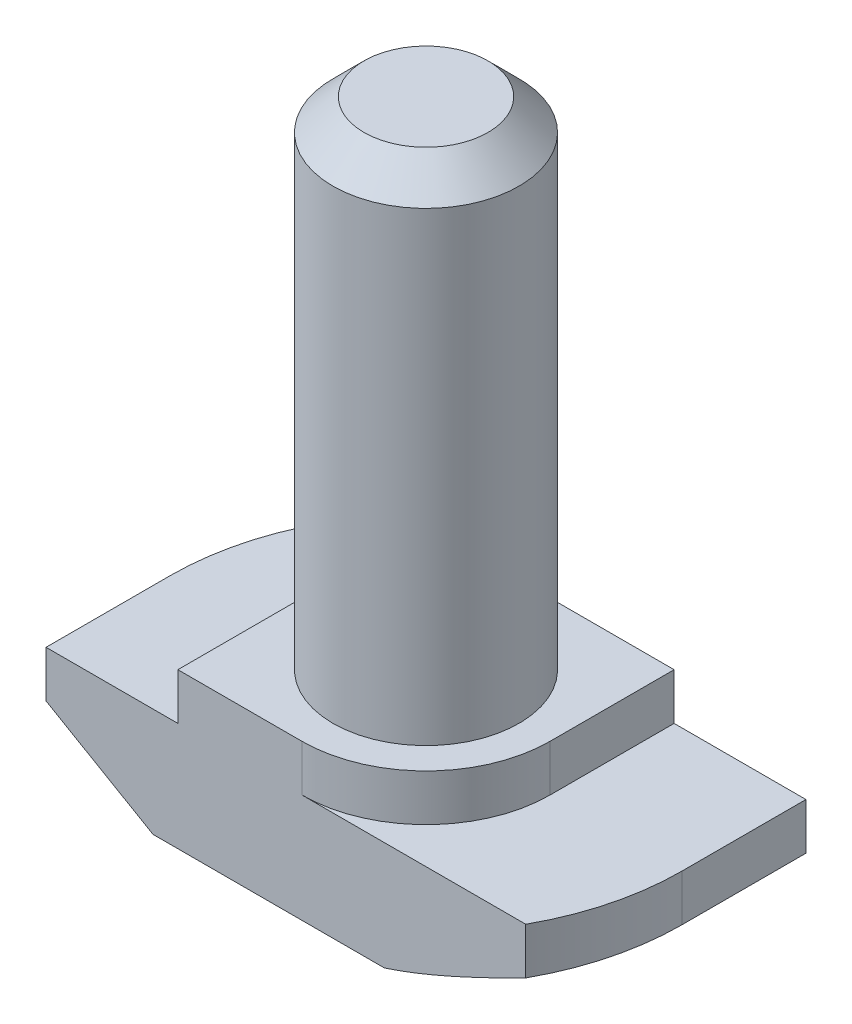
SolidWorks part; units mm, degrees
ref_plane "Спереди" through (0, 0, 0) normal (0, 0, 1) x (1, 0, 0)
ref_plane "Сверху" through (0, 0, 0) normal (0, 1, 0) x (1, 0, 0)
ref_plane "Справа" through (0, 0, 0) normal (1, 0, 0) x (0, 0, -1)
sketch "Эскиз1" plane through (0, 0, 0) normal (0, 0, 1) x (1, 0, 0)
  line L0 (8.25, 0) -> (-8.25, 0)
  line L1 (-8.25, 0) -> (-8.25, 3.5)
  line L2 (-8.25, 3.5) -> (-4, 3.5)
  line L3 (-4, 3.5) -> (-4, 5)
  line L4 (-4, 5) -> (4, 5)
  line L5 (0, 5) -> (0, 0) construction
  line L6 (4, 3.5) -> (4, 5)
  line L7 (8.25, 3.5) -> (4, 3.5)
  line L8 (8.25, 0) -> (8.25, 3.5)
  point P12 (-8.25, 2.6435)
  point P13 (-4, 3.6993)
  dimension "D1" = 8
  dimension "D2" = 16.5
  dimension "D3" = 5
  dimension "D4" = 1.5
extrude "Бобышка-Вытянуть1" add sketch "Эскиз1" along normal mid plane 8
sketch "Эскиз2" plane through (0, 5, 0) normal (0, 1, 0) x (1, 0, 0)
  circle A0 centre (0, 0) radius 3
  dimension "D1" = 6
extrude "Бобышка-Вытянуть2" add sketch "Эскиз2" along normal blind 16
cosmetic thread "Условное изображение резьбы1" parameters "D2"=4.891
sketch "Эскиз3" plane through (0, 5, 0) normal (0, 1, 0) x (1, 0, 0)
  line L0 (-4, -4) -> (-4, 4) construction
  line L1 (4, 4) -> (-4, 4) construction
  line L2 (-4, 0) -> (-4, 4)
  line L3 (-4, 4) -> (0, 4)
  line L4 (0, -4) -> (4, -4)
  line L5 (4, -4) -> (-4, -4) construction
  line L6 (4, -4) -> (4, 0)
  line L7 (4, -4) -> (4, 4) construction
  arc A0 (-4, 0) -> (0, 4) centre (0, 0) cw
  arc A1 (4, 0) -> (0, -4) centre (0, 0) cw
extrude "Вырез-Вытянуть1" cut sketch "Эскиз3" against normal up to surface (1.5 mm away) up to face at (-6.125, 3.5, 0)
sketch "Эскиз4" plane through (0, 3.5, 0) normal (0, 1, 0) x (1, 0, 0)
  line L0 (-8.25, -4) -> (-8.25, 4) construction
  line L1 (8.25, -4) -> (8.25, 4) construction
  line L2 (-7.2154, 4) -> (-8.25, 4)
  line L3 (-8.25, 4) -> (-8.25, 0)
  line L4 (7.2154, -4) -> (8.25, -4)
  line L5 (8.25, -4) -> (8.25, 0)
  arc A0 (-8.25, 0) -> (-7.2154, 4) centre (0, 0) cw
  arc A1 (8.25, 0) -> (7.2154, -4) centre (0, 0) cw
extrude "Вырез-Вытянуть2" cut sketch "Эскиз4" against normal through all
sketch "Эскиз5" plane through (0, 0, 4) normal (0, 0, 1) x (1, 0, 0)
  line L0 (-8.25, 2) -> (-4.8, 0)
  line L1 (-8.25, 3.5) -> (-8.25, 0) construction
  line L2 (-8.25, 0) -> (7.2154, 0) construction
  line L3 (-4.8, 0) -> (-8.25, 0)
  line L4 (-8.25, 0) -> (-8.25, 2)
  line L6 (-4, 3.5) -> (-8.25, 3.5) construction
  line L7 (-4, 5) -> (-4, 3.5) construction
  point P6 (-4.9519, 0)
  point P9 (0, 0)
  point P10 (-4.6154, 0)
  point P12 (-8.25, 2.2665)
  point P15 (0, 0)
  dimension "D1" = 1.5
  dimension "D2" = 0.8
sketch "Эскиз6" plane through (0, 0, 0) normal (0, -1, 0) x (1, 0, 0)
  line L0 (0, -8.25) -> (8.25, -8.25)
  line L1 (8.25, -8.25) -> (8.25, 0)
  line L2 (0, 8.25) -> (-8.25, 8.25)
  line L3 (-8.25, 8.25) -> (-8.25, 0)
  arc A0 (-8.25, 0) -> (0, -8.25) centre (0, 0) ccw
  arc A1 (8.25, 0) -> (0, 8.25) centre (0, 0) ccw
  point P10 (0, 0)
sweep "Вырез-По траектории1" cut profiles "Эскиз5" path "Эскиз6"
chamfer "Фаска2" distance 1 angle 45 1 edges at (0, 21, 3)
